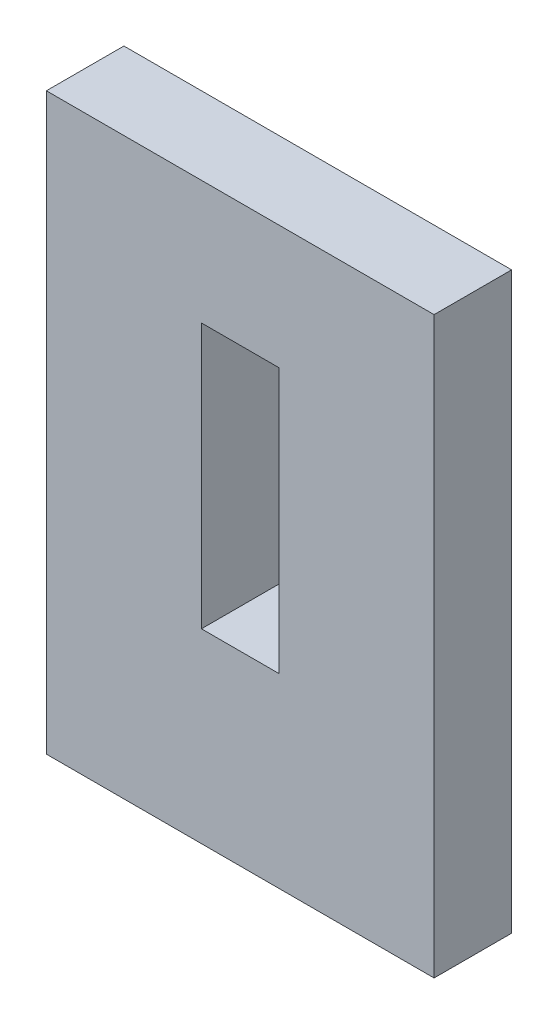
SolidWorks part; units mm, degrees
ref_plane "Front Plane" through (0, 0, 0) normal (0, 0, 1) x (1, 0, 0)
ref_plane "Top Plane" through (0, 0, 0) normal (0, 1, 0) x (1, 0, 0)
ref_plane "Right Plane" through (0, 0, 0) normal (1, 0, 0) x (0, 0, -1)
sketch "Sketch1" plane through (0, 0, 0) normal (0, 0, 1) x (1, 0, 0)
  line L1 (0, 0) -> (31.75, 0)
  line L2 (0, 0) -> (0, 47.0473)
  line L3 (0, 47.0473) -> (31.75, 47.0473)
  line L4 (31.75, 0) -> (31.75, 47.0473)
  line L5 (12.7, 15.24) -> (19.05, 15.24)
  line L6 (12.7, 15.24) -> (12.7, 36.9316)
  line L7 (12.7, 36.9316) -> (19.05, 36.9316)
  line L8 (19.05, 15.24) -> (19.05, 36.9316)
  point P9 (0, 0)
  dimension "D1" = 21.6916
  dimension "D2" = 6.35
  dimension "D3" = 12.7
  dimension "D4" = 12.7
  dimension "D5" = 15.24
extrude "Boss-Extrude1" add sketch "Sketch1" along normal blind 6.35
